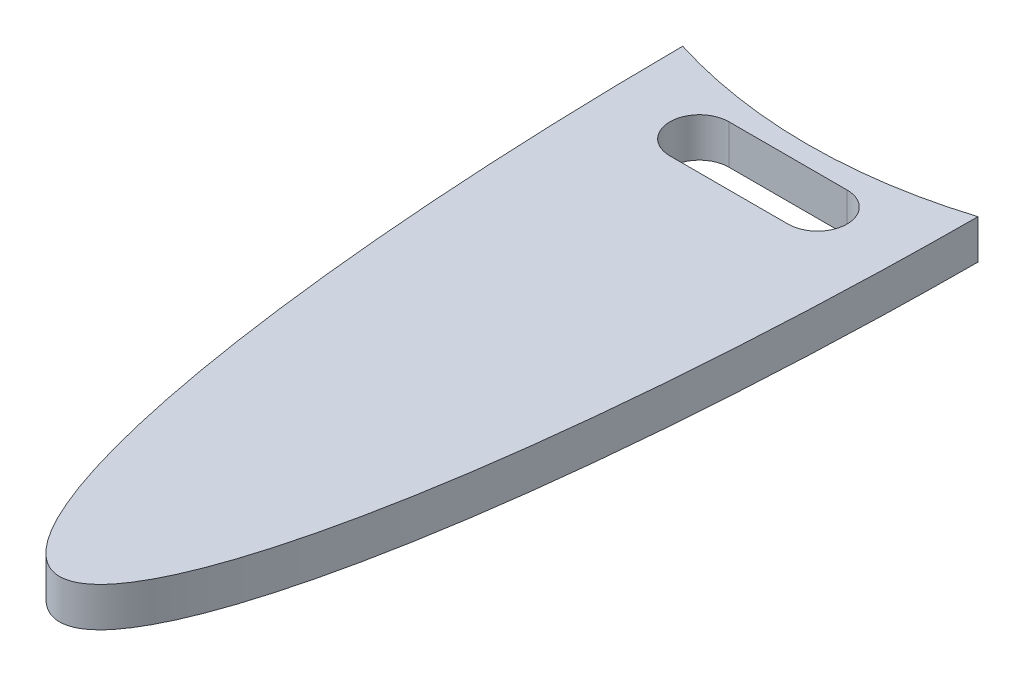
SolidWorks part; units mm, degrees
ref_plane "Front Plane" through (0, 0, 0) normal (0, 0, 1) x (1, 0, 0)
ref_plane "Top Plane" through (0, 0, 0) normal (0, 1, 0) x (1, 0, 0)
ref_plane "Right Plane" through (0, 0, 0) normal (1, 0, 0) x (0, 0, -1)
sketch "Sketch1" plane through (0, 0, 0) normal (0, 1, 0) x (1, 0, 0)
  line L0 (-9.525, 0) -> (9.525, 0)
  line L1 (0, 50.8) -> (0, -50.8) construction
  ellipse E0 centre (0, 0) end of major axis (0, 50.8) minor radius 9.525
  dimension "D1" = 19.05
  dimension "D2" = 101.6
extrude "Boss-Extrude1" add sketch "Sketch1" along normal blind 2.54 contours L0 L1 E0 | L1 L0 E0
sketch "Sketch3" plane through (0, 2.54, 0) normal (0, 1, 0) x (1, 0, 0)
  line L0 (-3.81, -5.715) -> (3.81, -5.715) construction
  line L1 (-3.81, -3.81) -> (3.81, -3.81)
  line L2 (-3.81, -7.62) -> (3.81, -7.62)
  line L3 (0, 0) -> (0, -50.8) construction
  line L4 (-9.525, 0) -> (9.525, 0) construction
  arc A0 (-3.81, -3.81) -> (-3.81, -7.62) centre (-3.81, -5.715) ccw
  arc A1 (3.81, -7.62) -> (3.81, -3.81) centre (3.81, -5.715) ccw
  ellipse E0 centre (0, 0) end of major axis (0, 50.8) minor radius 9.525 (-9.525, 0) -> (9.525, 0) ccw construction
  point P2 (0, -5.715)
  point P19 (0, -3.81)
  dimension "D1" = 0
  dimension "D2" = 3.81
  dimension "D3" = 3.81
  dimension "D4" = 7.62
extrude "Cut-Extrude1" cut sketch "Sketch3" against normal through all
sketch "Sketch4" plane through (0, 2.54, 0) normal (0, 1, 0) x (1, 0, 0)
  line L0 (0, 0) -> (0, -50.8) construction
  line L1 (0, -50.8) -> (0, 72.305) construction
  line L4 (-9.525, 0) -> (9.525, 0) construction
  circle A0 centre (0, 29.21) radius 31.75
  ellipse E0 centre (0, 0) end of major axis (0, 50.8) minor radius 9.525 (-9.525, 0) -> (9.525, 0) ccw construction
  point P15 (0, -1.0505)
  point P16 (-7.5785, 0)
  dimension "D1" = 63.5
  dimension "D2" = 0
  dimension "D3" = 29.21
extrude "Cut-Extrude2" cut sketch "Sketch4" against normal through all
